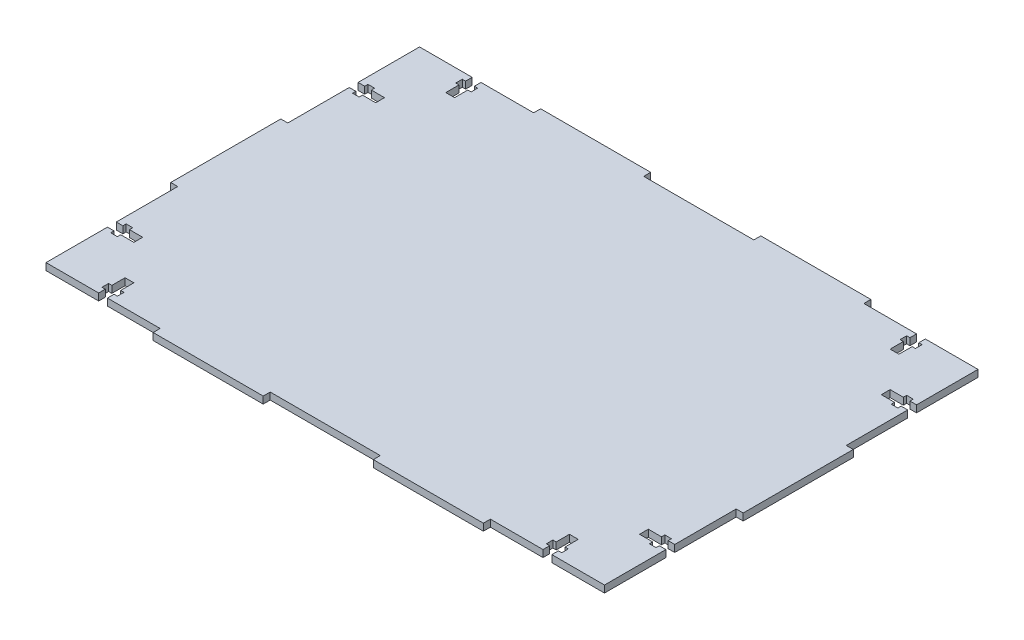
SolidWorks part; units mm, degrees
material "Acrylic (Medium-high impact)"
ref_plane "Front Plane" through (0, 0, 0) normal (0, 0, 1) x (1, 0, 0)
ref_plane "Top Plane" through (0, 0, 0) normal (0, 1, 0) x (1, 0, 0)
ref_plane "Right Plane" through (0, 0, 0) normal (1, 0, 0) x (0, 0, -1)
sketch "Sketch1" plane through (0, 0, 0) normal (0, 1, 0) x (1, 0, 0)
  line L0 (0, 172.825) -> (260, 172.825) construction
  line L1 (0, 0) -> (260, 0)
  line L2 (0, 0) -> (0, 176)
  line L3 (0, 176) -> (260, 176)
  line L4 (260, 0) -> (260, 176)
  line L5 (55, 176) -> (55, 172.825)
  line L6 (205, 176) -> (205, 172.825)
  line L7 (105, 172.825) -> (105, 176)
  line L8 (155, 172.825) -> (155, 176)
  line L9 (55, 172.825) -> (0, 172.825)
  line L10 (105, 172.825) -> (155, 172.825)
  line L11 (0, 3.175) -> (260, 3.175) construction
  line L12 (55, 3.175) -> (55, 0)
  line L13 (105, 3.175) -> (105, 0)
  line L14 (155, 0) -> (155, 3.175)
  line L15 (205, 3.175) -> (205, 0)
  line L16 (0, 3.175) -> (55, 3.175)
  line L17 (105, 3.175) -> (155, 3.175)
  line L18 (260, 172.825) -> (205, 172.825)
  line L19 (205, 3.175) -> (260, 3.175)
  line L20 (3.175, 176) -> (3.175, 0) construction
  line L21 (256.825, 176) -> (256.825, 0) construction
  line L22 (0, 113) -> (3.175, 113)
  line L23 (3.175, 63) -> (0, 63)
  line L24 (256.825, 113) -> (260, 113)
  line L25 (256.825, 63) -> (260, 63)
  line L26 (3.175, 113) -> (3.175, 172.825)
  line L27 (3.175, 3.175) -> (3.175, 63)
  line L28 (256.825, 3.175) -> (256.825, 63)
  line L29 (256.825, 113) -> (256.825, 172.825)
  point P37 (1.5875, 113)
  dimension "D1" = 176
  dimension "D2" = 260
  dimension "D3" = 3.175
  dimension "D4" = 55
  dimension "D5" = 55
  dimension "D6" = 50
  dimension "D7" = 50
  dimension "D8" = 50
  dimension "D9" = 3.175
  dimension "D10" = 63
  dimension "D11" = 50
  dimension "D12" = 63
  dimension "D13" = 3.175
  dimension "D14" = 3.175
extrude "Boss-Extrude1" add sketch "Sketch1" along normal mid plane 3.175
sketch "Sketch3" plane through (0, 1.5875, 0) normal (0, 1, 0) x (1, 0, 0)
  line L0 (29.0875, 3.175) -> (29.0875, 172.825) construction
  line L1 (205, 3.175) -> (256.825, 3.175) construction
  line L2 (25.5875, 166.825) -> (27.0875, 166.825)
  line L3 (27.0875, 169.825) -> (27.0875, 172.825)
  line L4 (31.0875, 169.825) -> (31.0875, 172.825)
  line L5 (27.0875, 169.825) -> (25.5875, 169.825)
  line L6 (25.5875, 169.825) -> (25.5875, 166.825)
  line L7 (256.825, 3.175) -> (256.825, 63) construction
  line L8 (256.825, 3.175) -> (256.825, 63)
  line L9 (130, 3.175) -> (130, 172.825) construction
  line L10 (105, 3.175) -> (155, 3.175) construction
  line L11 (105, 172.825) -> (155, 172.825) construction
  line L12 (260, 88) -> (0, 88) construction
  line L13 (260, 63) -> (260, 113) construction
  line L14 (205, 3.175) -> (256.825, 3.175)
  line L15 (0, 63) -> (0, 113) construction
  line L16 (256.825, 33.0875) -> (3.175, 33.0875) construction
  line L17 (256.825, 140.9125) -> (253.825, 140.9125)
  line L18 (230.9125, 3.175) -> (230.9125, 172.825) construction
  line L19 (253.825, 140.9125) -> (253.825, 139.4125)
  line L20 (234.4125, 9.175) -> (232.9125, 9.175)
  line L21 (232.9125, 6.175) -> (232.9125, 3.175)
  line L22 (228.9125, 6.175) -> (228.9125, 3.175)
  line L23 (232.9125, 6.175) -> (234.4125, 6.175)
  line L24 (234.4125, 6.175) -> (234.4125, 9.175)
  line L25 (227.4125, 9.175) -> (228.9125, 9.175)
  line L26 (228.9125, 9.175) -> (228.9125, 15.175)
  line L27 (227.4125, 6.175) -> (227.4125, 9.175)
  line L28 (228.9125, 6.175) -> (227.4125, 6.175)
  line L29 (228.9125, 15.175) -> (232.9125, 15.175)
  line L30 (232.9125, 15.175) -> (232.9125, 9.175)
  line L31 (256.825, 31.0875) -> (253.825, 31.0875)
  line L32 (253.825, 31.0875) -> (253.825, 29.5875)
  line L33 (253.825, 29.5875) -> (250.825, 29.5875)
  line L34 (250.825, 29.5875) -> (250.825, 31.0875)
  line L35 (250.825, 31.0875) -> (244.825, 31.0875)
  line L36 (244.825, 31.0875) -> (244.825, 35.0875)
  line L37 (250.825, 35.0875) -> (244.825, 35.0875)
  line L38 (250.825, 36.5875) -> (250.825, 35.0875)
  line L39 (253.825, 36.5875) -> (250.825, 36.5875)
  line L40 (253.825, 35.0875) -> (253.825, 36.5875)
  line L41 (256.825, 35.0875) -> (253.825, 35.0875)
  line L42 (253.825, 139.4125) -> (250.825, 139.4125)
  line L43 (250.825, 139.4125) -> (250.825, 140.9125)
  line L44 (250.825, 140.9125) -> (244.825, 140.9125)
  line L45 (244.825, 144.9125) -> (244.825, 140.9125)
  line L46 (250.825, 144.9125) -> (244.825, 144.9125)
  line L47 (250.825, 146.4125) -> (250.825, 144.9125)
  line L48 (253.825, 146.4125) -> (250.825, 146.4125)
  line L49 (253.825, 144.9125) -> (253.825, 146.4125)
  line L50 (256.825, 144.9125) -> (253.825, 144.9125)
  line L51 (232.9125, 160.825) -> (232.9125, 166.825)
  line L52 (228.9125, 160.825) -> (232.9125, 160.825)
  line L53 (228.9125, 169.825) -> (227.4125, 169.825)
  line L54 (227.4125, 169.825) -> (227.4125, 166.825)
  line L55 (228.9125, 166.825) -> (228.9125, 160.825)
  line L56 (227.4125, 166.825) -> (228.9125, 166.825)
  line L57 (234.4125, 169.825) -> (234.4125, 166.825)
  line L58 (232.9125, 169.825) -> (234.4125, 169.825)
  line L59 (228.9125, 169.825) -> (228.9125, 172.825)
  line L60 (232.9125, 169.825) -> (232.9125, 172.825)
  line L61 (234.4125, 166.825) -> (232.9125, 166.825)
  line L62 (256.825, 172.825) -> (205, 172.825) construction
  line L63 (3.175, 3.175) -> (3.175, 63) construction
  line L64 (32.5875, 166.825) -> (31.0875, 166.825)
  line L65 (31.0875, 166.825) -> (31.0875, 160.825)
  line L66 (32.5875, 169.825) -> (32.5875, 166.825)
  line L67 (31.0875, 169.825) -> (32.5875, 169.825)
  line L68 (31.0875, 160.825) -> (27.0875, 160.825)
  line L69 (27.0875, 160.825) -> (27.0875, 166.825)
  line L70 (3.175, 144.9125) -> (6.175, 144.9125)
  line L71 (6.175, 144.9125) -> (6.175, 146.4125)
  line L72 (6.175, 146.4125) -> (9.175, 146.4125)
  line L73 (9.175, 146.4125) -> (9.175, 144.9125)
  line L74 (9.175, 144.9125) -> (15.175, 144.9125)
  line L75 (15.175, 144.9125) -> (15.175, 140.9125)
  line L76 (9.175, 140.9125) -> (15.175, 140.9125)
  line L77 (9.175, 139.4125) -> (9.175, 140.9125)
  line L78 (6.175, 139.4125) -> (9.175, 139.4125)
  line L79 (3.175, 35.0875) -> (6.175, 35.0875)
  line L80 (6.175, 35.0875) -> (6.175, 36.5875)
  line L81 (6.175, 36.5875) -> (9.175, 36.5875)
  line L82 (9.175, 36.5875) -> (9.175, 35.0875)
  line L83 (9.175, 35.0875) -> (15.175, 35.0875)
  line L84 (15.175, 31.0875) -> (15.175, 35.0875)
  line L85 (9.175, 31.0875) -> (15.175, 31.0875)
  line L86 (9.175, 29.5875) -> (9.175, 31.0875)
  line L87 (6.175, 29.5875) -> (9.175, 29.5875)
  line L88 (6.175, 31.0875) -> (6.175, 29.5875)
  line L89 (3.175, 31.0875) -> (6.175, 31.0875)
  line L90 (27.0875, 15.175) -> (27.0875, 9.175)
  line L91 (31.0875, 15.175) -> (27.0875, 15.175)
  line L92 (31.0875, 6.175) -> (32.5875, 6.175)
  line L93 (32.5875, 6.175) -> (32.5875, 9.175)
  line L94 (31.0875, 9.175) -> (31.0875, 15.175)
  line L95 (32.5875, 9.175) -> (31.0875, 9.175)
  line L96 (25.5875, 6.175) -> (25.5875, 9.175)
  line L97 (27.0875, 6.175) -> (25.5875, 6.175)
  line L98 (31.0875, 6.175) -> (31.0875, 3.175)
  line L99 (27.0875, 6.175) -> (27.0875, 3.175)
  line L100 (25.5875, 9.175) -> (27.0875, 9.175)
  line L101 (6.175, 140.9125) -> (6.175, 139.4125)
  line L102 (3.175, 140.9125) -> (6.175, 140.9125)
  line L103 (3.175, 3.175) -> (3.175, 63)
  point P40 (244.825, 33.0875)
  point P45 (252.325, 36.5875)
  point P69 (244.825, 142.9125)
  point P70 (0, 0)
  point P73 (0, 0)
  point P128 (15.175, 142.9125)
  point P129 (15.175, 33.0875)
  line M30 (256.825, 113) -> (256.825, 172.825)
  line M31 (256.825, 172.825) -> (205, 172.825)
  line M39 (55, 172.825) -> (3.175, 172.825)
  line M40 (3.175, 172.825) -> (3.175, 113)
  line M44 (3.175, 63) -> (3.175, 3.175)
  line M45 (3.175, 3.175) -> (55, 3.175)
  dimension "D1" = 4
  dimension "D2" = 12
  dimension "D3" = 3
  dimension "D4" = 7
  dimension "D5" = 3
  dimension "D7" = 3
  dimension "D8" = 3
  dimension "D9" = 12
  dimension "D10" = 4
  dimension "D11" = 7
extrude "Cut-Extrude1" cut sketch "Sketch3" against normal through all both and the other way through all contours L30 L29 L26 L25 L27 L28 L22 L14 L21 L23 L24 L20 | L8 L41 L40 L39 L38 L37 L36 L35 L34 L33 L32 L31 | L50 L49 L48 L47 L46 L45 L44 L43 L42 L19 L17 M30 | L61 L57 L58 L60 L59 L53 L54 L56 L55 L52 L51 M31 | L69 L68 L65 L64 L66 L67 L4 L3 L5 L6 L2 M39 | L102 L101 L78 L77 L76 L75 L74 L73 L72 L71 L70 M40 | L89 L88 L87 L86 L85 L84 L83 L82 L81 L80 L79 M44 | L100 L96 L97 L99 L98 L92 L93 L95 L94 L91 L90 M45
